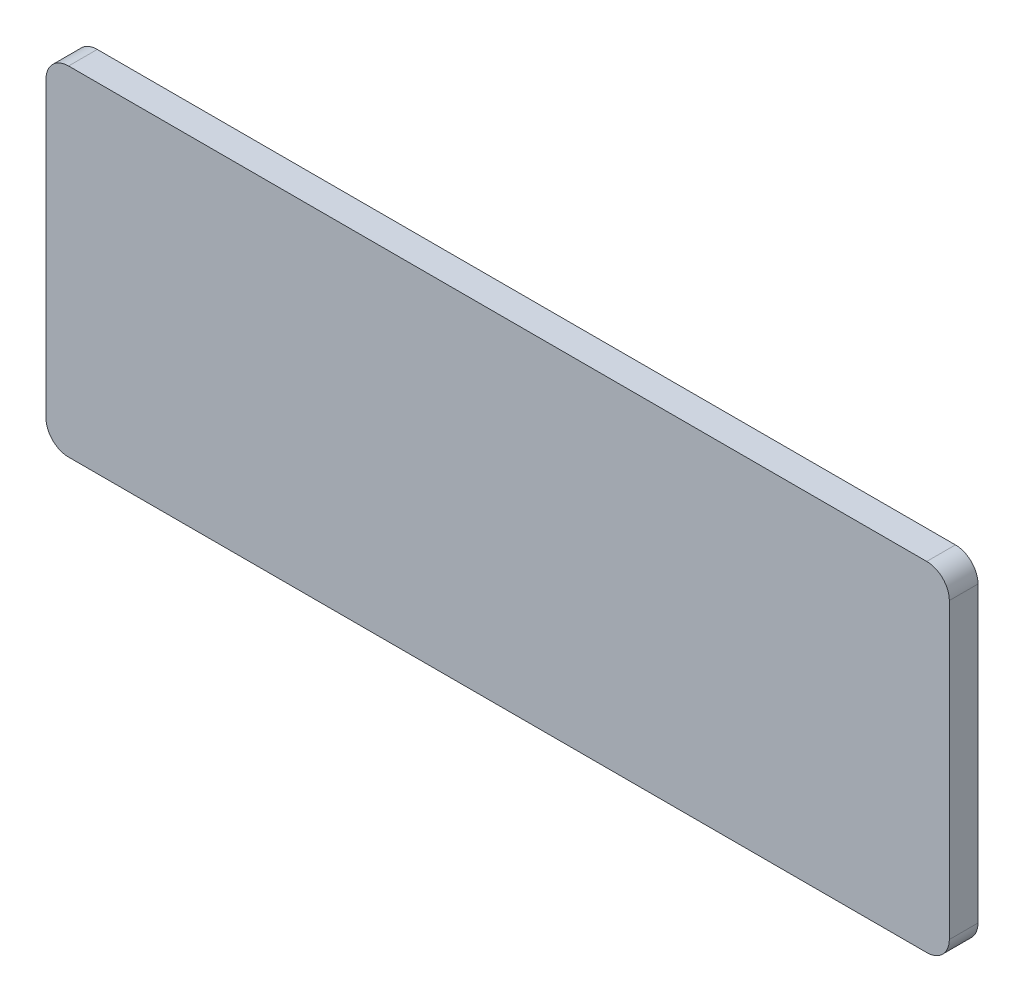
SolidWorks part; units mm, degrees
material "Maple"
ref_plane "Front Plane" through (0, 0, 0) normal (0, 0, 1) x (1, 0, 0)
ref_plane "Top Plane" through (0, 0, 0) normal (0, 1, 0) x (1, 0, 0)
ref_plane "Right Plane" through (0, 0, 0) normal (1, 0, 0) x (0, 0, -1)
sketch "Sketch1" plane through (0, 0, 0) normal (0, 0, 1) x (1, 0, 0)
  line L1 (-100, 37.5) -> (100, 37.5)
  line L2 (-100, 37.5) -> (-100, -37.5)
  line L3 (-100, -37.5) -> (100, -37.5)
  line L4 (100, 37.5) -> (100, -37.5)
  line L5 (-100, 37.5) -> (100, -37.5) construction
  line L6 (-100, -37.5) -> (100, 37.5) construction
  point P0 (0, 0)
  dimension "D1" = 200
  dimension "D2" = 75
extrude "Boss-Extrude1" add sketch "Sketch1" against normal blind 6.35
fillet "Fillet1" radius 5 4 edges at (-100, -37.5, -3.175) (100, -37.5, -3.175) (100, 37.5, -3.175) (-100, 37.5, -3.175)
